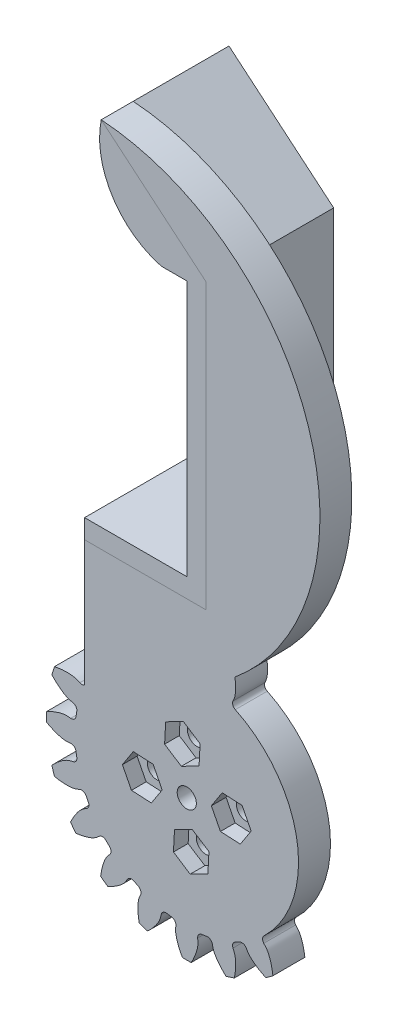
SolidWorks part; units mm, degrees
ref_plane "前视基准面" through (0, 0, 0) normal (0, 0, 1) x (1, 0, 0)
ref_plane "上视基准面" through (0, 0, 0) normal (0, 1, 0) x (1, 0, 0)
ref_plane "右视基准面" through (0, 0, 0) normal (1, 0, 0) x (0, 0, -1)
ref_axis "Axis1" through (0, 0, -88.99) along (0, 0, 1)
sketch "草图1" plane through (0, 0, 0) normal (0, 0, 1) x (1, 0, 0)
  circle A0 centre (0, 0) radius 22
extrude "LaShenA" add sketch "草图1" along normal blind 5
sketch "SketchA" plane through (0, 0, 5) normal (0, 0, 1) x (1, 0, 0)
  line L0 (0, 0) -> (0, 22) construction
  arc A0 (-2.3563, 17.3406) -> (-3.1175, 17.2201) centre (0, 0) ccw
  arc A1 (-0.0193, 23.0469) -> (-7.1036, 21.9249) centre (0, 0) ccw
  arc A2 (-3.1175, 17.2201) -> (-3.9948, 17.8031) centre (-3.2529, 17.9679) cw
  arc A3 (-1.7022, 18.1662) -> (-2.3563, 17.3406) centre (-2.4587, 18.0937) cw
  circle A4 centre (0, 0) radius 18.7939 construction
  circle A5 centre (0, 0) radius 22 construction
  circle A6 centre (0, 0) radius 17.5 construction
  circle A7 centre (0, 0) radius 20 construction
  spline S0 degree 3 poles (-1.7022, 18.1662) (-1.7197, 18.3492) (-1.753, 18.5872) (-1.755, 18.8544) (-1.7481, 18.9686) (-1.7404, 19.0593) (-1.7286, 19.1637) (-1.7121, 19.2816) (-1.69, 19.4129) (-1.6617, 19.5572) (-1.6263, 19.7144) (-1.5833, 19.8841) (-1.5318, 20.0661) (-1.4712, 20.2599) (-1.4008, 20.4653) (-1.3199, 20.6818) (-1.2279, 20.9091) (-1.1241, 21.1465) (-1.0079, 21.3937) (-0.8787, 21.6502) (-0.736, 21.9154) (-0.579, 22.1887) (-0.3453, 22.5712) (-0.1542, 22.8564) (-0.0193, 23.0469) knots 0.125068 0.125068 0.125068 0.125068 0.215847 0.244833 0.257593 0.272674 0.290074 0.309794 0.331834 0.356194 0.382875 0.411875 0.443195 0.476835 0.512796 0.551076 0.591676 0.634597 0.679837 0.727398 0.777278 0.829478 0.883999 1 1 1 1
  spline S1 degree 3 poles (-3.9948, 17.8031) (-4.0347, 17.9825) (-4.0765, 18.2192) (-4.1572, 18.474) (-4.1991, 18.5804) (-4.2344, 18.6643) (-4.2779, 18.76) (-4.33, 18.867) (-4.3916, 18.985) (-4.4632, 19.1135) (-4.5453, 19.252) (-4.6387, 19.4001) (-4.7439, 19.5573) (-4.8615, 19.723) (-4.9919, 19.8965) (-5.1357, 20.0775) (-5.2935, 20.2651) (-5.4655, 20.4589) (-5.6524, 20.6581) (-5.8546, 20.8621) (-6.0723, 21.0702) (-6.306, 21.2817) (-6.6465, 21.5732) (-6.9163, 21.7854) (-7.1036, 21.9249) knots 0.125068 0.125068 0.125068 0.125068 0.215847 0.244833 0.257593 0.272674 0.290074 0.309794 0.331834 0.356194 0.382875 0.411875 0.443195 0.476835 0.512796 0.551076 0.591676 0.634597 0.679837 0.727398 0.777278 0.829478 0.883999 1 1 1 1
  dimension "D1" = 0.76
  dimension "Db" = 37.5877
  dimension "Da" = 44
  dimension "Df" = 35
  dimension "Dn" = 40
extrude "Cut-ExtrudeA" cut sketch "SketchA" against normal blind 50
pattern_circular "www.KYTool.cn" count 20 over 360 about axis through (0, 0, -88.99) along (0, 0, 1) of "Cut-ExtrudeA"
sketch "草图3" plane through (0, 0, 0) normal (0, 0, -1) x (-1, 0, 0)
  line L0 (16, 27) -> (16, 30)
  line L1 (16, 30) -> (0, 30)
  line L2 (0, 30) -> (0, 70.1)
  line L3 (0, 70.1) -> (15.3209, 82.9558) construction
  line L5 (13, 27) -> (-3, 27)
  line L6 (-3, 27) -> (-3, 71.4989)
  line L7 (-3, 71.4989) -> (13.3925, 85.2539)
  line L8 (0, 70.1) -> (4, 70.1)
  line L9 (13, 27) -> (16, 27)
  line L11 (13, 0) -> (13, 27) construction
  line L13 (16, 0) -> (16, 30) construction
  arc A1 (16, 0) -> (13, 9.3274) centre (0, 0) ccw construction
  arc A2 (4, 70.1) -> (13.3925, 85.2539) centre (0.6535, 82.6619) ccw
  arc A3 (13, 9.3274) -> (16, 0) centre (0, 0) ccw construction
  dimension "D2" = 32
  dimension "D10" = 13
  dimension "D3" = 30
  dimension "D4" = 16
  dimension "D5" = 40.1
  dimension "D6" = 130
  dimension "D7" = 20
  dimension "D9" = 4
  dimension "D8" = 3
extrude "凸台-拉伸2" add sketch "草图3" along normal blind 15 and the other way blind 5 separate body contours L8 A2 L7 L6 L5 L9 L0 L1 L2
sketch "草图4" plane through (0, 0, 0) normal (0, 0, -1) x (-1, 0, 0)
  line L0 (16, 28.5) -> (16, 48.5) construction
  line L1 (16, 27) -> (16, 30) construction
  line L2 (16, 27) -> (16, 6.98)
  line L3 (16, 6.98) -> (11.9, 6.98)
  line L4 (11.9, 6.98) -> (11.9, 11.8826)
  line L5 (16, 27) -> (-3, 27) construction
  line L6 (-3, 27) -> (-3, 71.4989) construction
  line L7 (-3, 71.4989) -> (13.3925, 85.2539) construction
  line L8 (16, 27) -> (-3, 27)
  line L9 (-3, 27) -> (-3, 71.4989)
  line L10 (-3, 71.4989) -> (13.3925, 85.2539)
  arc A0 (13.3925, 85.2539) -> (11.9, 11.8826) centre (16, 48.5) ccw
  point P5 (13.3925, 85.2539)
  dimension "D1" = 20
extrude "凸台-拉伸3" add sketch "草图4" against normal blind 5
sketch "草图5" plane through (0, 0, 0) normal (0, 0, -1) x (-1, 0, 0)
  line L0 (-8.968, 20.5523) -> (-7.9448, 15.5926)
  line L2 (-8.968, 20.5523) -> (-16.1954, 18.5363)
  line L4 (-29.9806, -2.0094) -> (-16.762, -17.4153)
  line L5 (-16.762, -17.4153) -> (-12.3744, -12.3744)
  line L6 (-16.1954, 18.5363) -> (-29.9806, -2.0094)
  line L7 (16, 13.2346) -> (16, 9.4759)
  line L8 (16, 9.4759) -> (20.7167, 9.8274)
  line L9 (20.7167, 9.8274) -> (20.7167, 14.8436)
  line L10 (20.7167, 14.8436) -> (16, 13.2346)
  arc A0 (-12.3744, -12.3744) -> (-7.9448, 15.5926) centre (0, 0) cw
  circle A1 centre (-6.9657, 0.6925) radius 1.5
  circle A2 centre (0.6925, 6.9657) radius 1.5
  circle A3 centre (6.9657, -0.6925) radius 1.5
  circle A4 centre (-0.6925, -6.9657) radius 1.5
  circle A5 centre (0, 0) radius 1.5
  arc A7 (-12.6438, -12.0989) -> (-12.0989, -12.6438) centre (0, 0) ccw construction
  arc A8 (-7.5996, 15.7638) -> (-8.2862, 15.4139) centre (0, 0) ccw construction
  point P7 (0, 0)
  point P18 (0, 0)
  dimension "D1" = 7
  dimension "D2" = 3
  dimension "D4" = 3
  dimension "D3" = 4
extrude "切除-拉伸2" cut sketch "草图5" against normal blind 5
sketch "草图7" plane through (0, 0, 5) normal (0, 0, 1) x (1, 0, 0)
  line L0 (5.2692, -1.9232) -> (8.3827, -2.0845)
  line L1 (1.9232, 5.2692) -> (2.0845, 8.3827)
  line L2 (2.0845, 8.3827) -> (-0.5312, 10.0792)
  line L3 (-0.5312, 10.0792) -> (-3.3082, 8.6621)
  line L4 (-3.3082, 8.6621) -> (-3.4696, 5.5486)
  line L5 (-3.4696, 5.5486) -> (-0.8538, 3.8521)
  line L6 (-0.8538, 3.8521) -> (1.9232, 5.2692)
  line L7 (8.3827, -2.0845) -> (10.0792, 0.5312)
  line L8 (10.0792, 0.5312) -> (8.6621, 3.3082)
  line L9 (8.6621, 3.3082) -> (5.5486, 3.4696)
  line L10 (5.5486, 3.4696) -> (3.8521, 0.8538)
  line L11 (3.8521, 0.8538) -> (5.2692, -1.9232)
  line L12 (-1.9232, -5.2692) -> (-2.0845, -8.3827)
  line L13 (-2.0845, -8.3827) -> (0.5312, -10.0792)
  line L14 (0.5312, -10.0792) -> (3.3082, -8.6621)
  line L15 (3.3082, -8.6621) -> (3.4696, -5.5486)
  line L16 (3.4696, -5.5486) -> (0.8538, -3.8521)
  line L17 (0.8538, -3.8521) -> (-1.9232, -5.2692)
  line L18 (-5.2692, 1.9232) -> (-8.3827, 2.0845)
  line L19 (-8.3827, 2.0845) -> (-10.0792, -0.5312)
  line L20 (-10.0792, -0.5312) -> (-8.6621, -3.3082)
  line L21 (-8.6621, -3.3082) -> (-5.5486, -3.4696)
  line L22 (-5.5486, -3.4696) -> (-3.8521, -0.8538)
  line L23 (-3.8521, -0.8538) -> (-5.2692, 1.9232)
  circle A0 centre (-0.6925, 6.9657) radius 2.7 construction
  point P30 (0, 0)
  dimension "D1" = 5.4
  dimension "D2" = 4
extrude "切除-拉伸4" cut sketch "草图7" against normal blind 2.3
